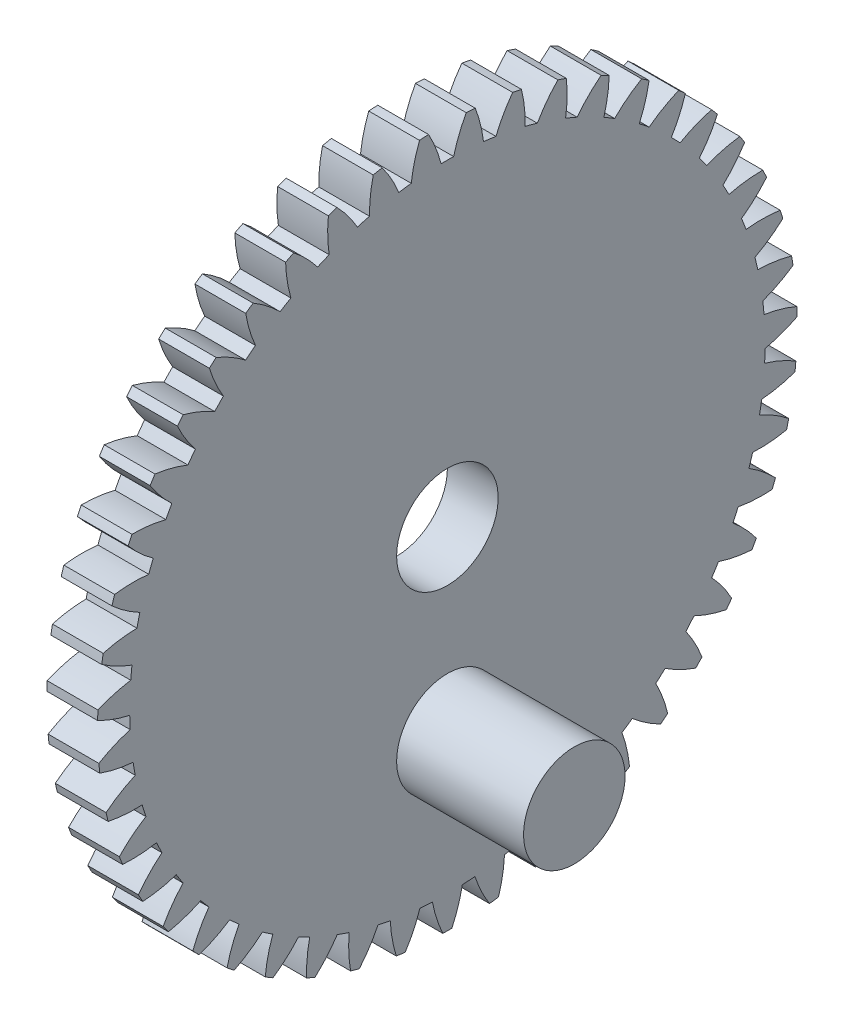
SolidWorks part; units mm, degrees
ref_plane "Plane1" through (0, 0, 0) normal (0, 0, 1) x (1, 0, 0)
ref_plane "Plane2" through (0, 0, 0) normal (0, 1, 0) x (1, 0, 0)
ref_plane "Plane3" through (0, 0, 0) normal (1, 0, 0) x (0, 0, -1)
sketch "HoldingSke" plane through (0, 0, 0) normal (0, 1, 0) x (1, 0, 0)
  line L0 (0, 0) -> (0.6062, -0.6501)
  line L1 (-15, 0) -> (100, 0) construction
  line L2 (0, 0) -> (-2.1039, 2.3779)
  line L3 (0, 0) -> (-11.863, 4.5341)
  line L4 (0, 0) -> (5.8897, 6.316)
  line L5 (0, 0) -> (-46.8476, -17.4728)
  line L6 (0, 0) -> (-3.3159, -2.2372)
  line L7 (-2.1039, 2.3779) -> (8.6586, 51.2059)
  line L8 (-76.2, 54.61) -> (-74.8, 54.61)
  line L9 (-71.009, 38.7566) -> (-53.1078, 45.2721)
  line L10 (-76.2, 71.12) -> (104.1128, 71.12)
  line L11 (0, 0) -> (-4, 0)
  line L12 (-76.2, 101.6) -> (-76.158, 101.6)
  line L13 (24.9733, 27.94) -> (52.9518, 28.4284)
  line L14 (24.9733, 27.94) -> (24.9743, 27.94)
  line L15 (24.9733, 27.94) -> (100.4006, 29.5858)
  line L16 (-63.627, -1.125) -> (-12.827, -1.125)
  circle A0 centre (0, 0) radius 4
  circle A1 centre (0, 0) radius 25.0302
  circle A2 centre (0, 0) radius 37.5
  circle A3 centre (0, 0) radius 4
  dimension "MHD" = 50.0605
  dimension "Hub_dia" = 75
  dimension "Bore" = 8
  dimension "MBD" = 8
  dimension "Num_teeth" = 47
  dimension "Pitch" = 0.8889
  dimension "Overall_len" = 50
  dimension "Show_teeth" = 47
  dimension "Thickness" = 4
  dimension "OAL" = 50.0001
  dimension "T_dim" = 1.4
  dimension "Ap" = 20
  dimension "H" = 19.05
  dimension "Pitch_radius" = 180.3128
  dimension "Width" = 4
  dimension "Backlash" = 0.042
  dimension "Addendum_fac" = 1
  dimension "Dedendum_fac" = 1.25
  dimension "Clearance_fac" = 0.25
  dimension "Dedendum_add" = 0.001
  dimension "Module" = 1.125
sketch "BasProSke" plane through (0, 0, 0) normal (0, 1, 0) x (1, 0, 0)
  line L0 (-10, 0) -> (60, 0) construction
  line L1 (0, 0) -> (0, 27.5625)
  line L2 (0, 0) -> (4, 0)
  line L3 (4, 0) -> (4, 27.5625)
  line L4 (4, 27.5625) -> (0, 27.5625)
  dimension "Thickness" = 4
  dimension "Diameter" = 55.125
revolve "Base-Revolve" add sketch "BasProSke" angle 360 about L0
sketch "TooCutSke" plane through (0, 0, 0) normal (1, 0, 0) x (0, 0, -1)
  line L1 (0, 0) -> (0, 107) construction
  line L2 (0, 0) -> (-0.9569, 26.4202) construction
  line L3 (0, 0) -> (-3.53, 52.7322) construction
  line L4 (-0.9569, 26.4202) -> (-1.765, 26.3661) construction
  arc A0 (0.4944, 25.0254) -> (-0.4944, 25.0254) centre (0, 0) ccw
  arc A1 (1.4998, 27.5471) -> (-1.4998, 27.5471) centre (0, 0) ccw
  circle A2 centre (0, 0) radius 26.4375 construction
  circle A3 centre (0, 0) radius 24.8431 construction
  arc A4 (-0.4944, 25.0254) -> (-1.4998, 27.5471) centre (-10.7388, 22.4022) ccw
  arc A5 (1.4998, 27.5471) -> (0.4944, 25.0254) centre (10.7388, 22.4022) ccw
  dimension "Root_dia" = 50.0605
  dimension "Overcut_dia" = 55.1758
  dimension "Pitch_dia" = 52.875
  dimension "Base_dia" = 49.6862
  dimension "Flank_rad" = 10.575
  dimension "Half_ang" = 3.83
  dimension "Half_CT" = 0.8099
extrude "ToothCut" cut sketch "TooCutSke" along normal through all
fillet "Breaks" [suppressed] radius 0.0225
fillet "RootFillets" [suppressed] radius 0.2823
pattern_circular "TeethCuts" count 47 every 7.66 about axis through (-10, 0, 0) along (1, 0, 0) of "ToothCut", "RootFillets", "Breaks"
sketch "HubNeaOneSke" plane through (0, 0, 0) normal (-1, 0, 0) x (0, 0, 1)
  circle A0 centre (0, 0) radius 25.0302
  dimension "Diameter" = 50.0605
extrude "HubNearOne" [suppressed] add sketch "HubNeaOneSke" along normal blind 46.0001
sketch "HubNeaBotSke" plane through (0, 0, 0) normal (-1, 0, 0) x (0, 0, 1)
  circle A0 centre (0, 0) radius 25.0302
  dimension "Diameter" = 50.0605
extrude "HubNearBoth" [suppressed] add sketch "HubNeaBotSke" along normal blind 23
ref_plane "FarPln" through (4, 0, 0) normal (1, 0, 0) x (0, 0, -1)
sketch "HubFarSke" plane through (4, 0, 0) normal (1, 0, 0) x (0, 0, -1)
  circle A0 centre (0, 0) radius 25.0302
  dimension "Diameter" = 50.0605
extrude "HubFar" [suppressed] add sketch "HubFarSke" along normal blind 23
sketch "BorSke" plane through (0, 0, 0) normal (1, 0, 0) x (0, 0, -1)
  circle A0 centre (0, 0) radius 4
  dimension "Diameter" = 8
extrude "Bore" cut sketch "BorSke" along normal mid plane 100.0001
sketch "KeySke" plane through (0, 0, 0) normal (1, 0, 0) x (0, 0, -1)
  line L0 (-1.5, 0) -> (-1.5, 5.4)
  line L1 (-1.5, 5.4) -> (1.5, 5.4)
  line L2 (1.5, 5.4) -> (1.5, 0)
  line L3 (0, 0) -> (0, 34) construction
  line L4 (-1.5, 0) -> (1.5, 0)
  dimension "Offset" = 5.4
  dimension "Width" = 3
extrude "Keyway" [suppressed] cut sketch "KeySke" along normal mid plane 100.0001
pattern_circular "Keyway2" [suppressed] count 2 every 90 about axis through (-10, 0, 0) along (1, 0, 0)
sketch "Sketch1" plane through (4, 0, 0) normal (1, 0, 0) x (0, 0, -1)
  circle A0 centre (0, -14) radius 4
  circle A1 centre (0, 0) radius 4 construction
  dimension "D1" = 8
  dimension "D2" = 14
extrude "Boss-Extrude1" add sketch "Sketch1" along normal blind 10
equation "' \"Module@HoldingSke\" = 6.35"
equation "' \"Num_teeth@HoldingSke\" = 12"
equation "' \"Ap@HoldingSke\" =  20"
equation "' \"Ap@HoldingSke\" = 20"
equation "' \"Width@HoldingSke\" = 0.5 * 25.4"
equation "' \"Hub_dia@HoldingSke\"= 1 * 25.4"
equation "' \"Hub_dia@HoldingSke\" = 1 * 25.4"
equation "' \"Overall_len@HoldingSke\" = 1.0 * 25.4"
equation "' \"Bore@HoldingSke\" = 0.75 * 25.4"
equation "' \"T_dim@HoldingSke\" = 0.1 * 25.4"
equation "' \"Width@KeySke\" = 0.25 * 25.4"
equation "' \"Show_teeth@HoldingSke\" = 13"
equation "' \"Backlash@HoldingSke\" = 0.009 * 25.4"
equation "' \"Addendum_fac@HoldingSke\" = 1.0"
equation "' \"Dedendum_fac@HoldingSke\" = 1.25"
equation "' \"Dedendum_add@HoldingSke\" = 0.00005 * 25.4"
equation "' \"Clearance_fac@HoldingSke\" = 0.25"
equation "\"Pitch@HoldingSke\" = 1 / \"Module@HoldingSke\""
equation "\"Overcut_dia@TooCutSke\" = (\"Num_teeth@HoldingSke\" + 2 * \"Addendum_fac@HoldingSke\") / \"Pitch@HoldingSke\" + 0.002 * 25.4"
equation "\"Pitch_dia@TooCutSke\" = \"Num_teeth@HoldingSke\" / \"Pitch@HoldingSke\""
equation "\"Base_dia@TooCutSke\" = \"Num_teeth@HoldingSke\" / \"Pitch@HoldingSke\" * cos((\"Ap@HoldingSke\"  * 3.14159265 / 180))"
equation "\"Root_dia@TooCutSke\" = (\"Num_teeth@HoldingSke\" + 2) / \"Pitch@HoldingSke\" - 2 * (\"Addendum_fac@HoldingSke\" + \"Dedendum_fac@HoldingSke\") / \"Pitch@HoldingSke\" - \"Dedendum_add@HoldingSke\" * 2"
equation "\"Half_ang@TooCutSke\" = 180 / \"Num_teeth@HoldingSke\""
equation "\"Half_CT@TooCutSke\" = \"Num_teeth@HoldingSke\" / \"Pitch@HoldingSke\" * sin((3.14159265 / 2 / \"Num_teeth@HoldingSke\")) / 2 - 7 * \"Backlash@HoldingSke\" / 4"
equation "\"Flank_rad@TooCutSke\" = \"Num_teeth@HoldingSke\" / \"Pitch@HoldingSke\" / 5"
equation "\"Radius@RootFillets\" = \"Clearance_fac@HoldingSke\" / \"Pitch@HoldingSke\" + \"Dedendum_add@HoldingSke\""
equation "\"Break_rad@Breaks\" = 0.02 / \"Pitch@HoldingSke\""
equation "\"Thickness@HoldingSke\" = \"Width@HoldingSke\""
equation "\"OAL@HoldingSke\" = \"Thickness@HoldingSke\""
equation "\"MHD@HoldingSke\" = (\"Num_teeth@HoldingSke\" + 2) / \"Pitch@HoldingSke\" - 2 * (\"Addendum_fac@HoldingSke\" + \"Dedendum_fac@HoldingSke\")  / \"Pitch@HoldingSke\" - \"Dedendum_add@HoldingSke\" * 2"
equation "\"MBD@HoldingSke\" = (\"Num_teeth@HoldingSke\" + 2) / \"Pitch@HoldingSke\" - 2 * (\"Addendum_fac@HoldingSke\" + \"Dedendum_fac@HoldingSke\")  / \"Pitch@HoldingSke\" - \"Dedendum_add@HoldingSke\" * 2 - 0.002 * 25.4"
equation "\"MHD@HoldingSke\" = ((sgn( \"MHD@HoldingSke\" - \"Hub_dia@HoldingSke\" )-1)*( \"MHD@HoldingSke\" - \"Hub_dia@HoldingSke\" ))/-2+ \"Hub_dia@HoldingSke\""
equation "\"MBD@HoldingSke\" = ((sgn( \"MBD@HoldingSke\" - \"Bore@HoldingSke\" )-1)*( \"MBD@HoldingSke\" - \"Bore@HoldingSke\" ))/-2+ \"Bore@HoldingSke\""
equation "\"OAL@HoldingSke\" = ((sgn( \"OAL@HoldingSke\" - \"Overall_len@HoldingSke\" )+1)*( \"OAL@HoldingSke\" - \"Overall_len@HoldingSke\" ))/2 + \"Overall_len@HoldingSke\" + 0.000002 * 25.4"
equation "\"Num_teeth@TeethCuts\" = int( \"Show_teeth@HoldingSke\" ) + 1"
equation "\"Num_teeth@TeethCuts\" = ((sgn( \"Num_teeth@TeethCuts\" - \"Num_teeth@HoldingSke\" )-1)*( \"Num_teeth@TeethCuts\" - \"Num_teeth@HoldingSke\" ))/-2+ \"Num_teeth@HoldingSke\""
equation "\"Num_teeth@TeethCuts\" = ((sgn( \"Num_teeth@TeethCuts\" - 2.0)+1)*( \"Num_teeth@TeethCuts\" - 2.0))/2 +2.0"
equation "\"Angle@TeethCuts\" = 360.0 / \"Num_teeth@HoldingSke\""
equation "\"Diameter@BasProSke\" = (\"Num_teeth@HoldingSke\" + 2 * \"Addendum_fac@HoldingSke\") / \"Pitch@HoldingSke\""
equation "\"Thickness@BasProSke\"  = \"Thickness@HoldingSke\""
equation "' \"Fillet_rad@BasProSke\" =  \"Thickness@HoldingSke\" * 0.05"
equation "' \"Fillet_rad@BasProSke\" = \"Thickness@HoldingSke\" * 0.05"
equation "\"MHD@HoldingSke\" = ((sgn( \"MHD@HoldingSke\" - \"Root_dia@TooCutSke\" )-1)*( \"MHD@HoldingSke\" - \"Root_dia@TooCutSke\" ))/-2+ \"Root_dia@TooCutSke\""
equation "\"Diameter@HubNeaOneSke\" = \"MHD@HoldingSke\""
equation "\"Length@HubNearOne\" = \"OAL@HoldingSke\" - \"Thickness@BasProSke\""
equation "\"Diameter@HubNeaBotSke\" = \"MHD@HoldingSke\""
equation "\"Length@HubNearBoth\" = ( \"OAL@HoldingSke\" - \"Thickness@BasProSke\" ) / 2.0"
equation "\"Thickness@FarPln\" = \"Thickness@BasProSke\""
equation "\"Diameter@HubFarSke\" = \"MHD@HoldingSke\""
equation "\"Length@HubFar\" = ( \"OAL@HoldingSke\" - \"Thickness@BasProSke\" ) / 2.0"
equation "\"Diameter@BorSke\" = \"MBD@HoldingSke\""
equation "\"D1@Bore\" = \"OAL@HoldingSke\" * 2.0"
equation "\"D1@Keyway\" = \"OAL@HoldingSke\" * 2.0"
equation "\"Offset@KeySke\" = \"T_dim@HoldingSke\" + \"MBD@HoldingSke\" / 2.0"
